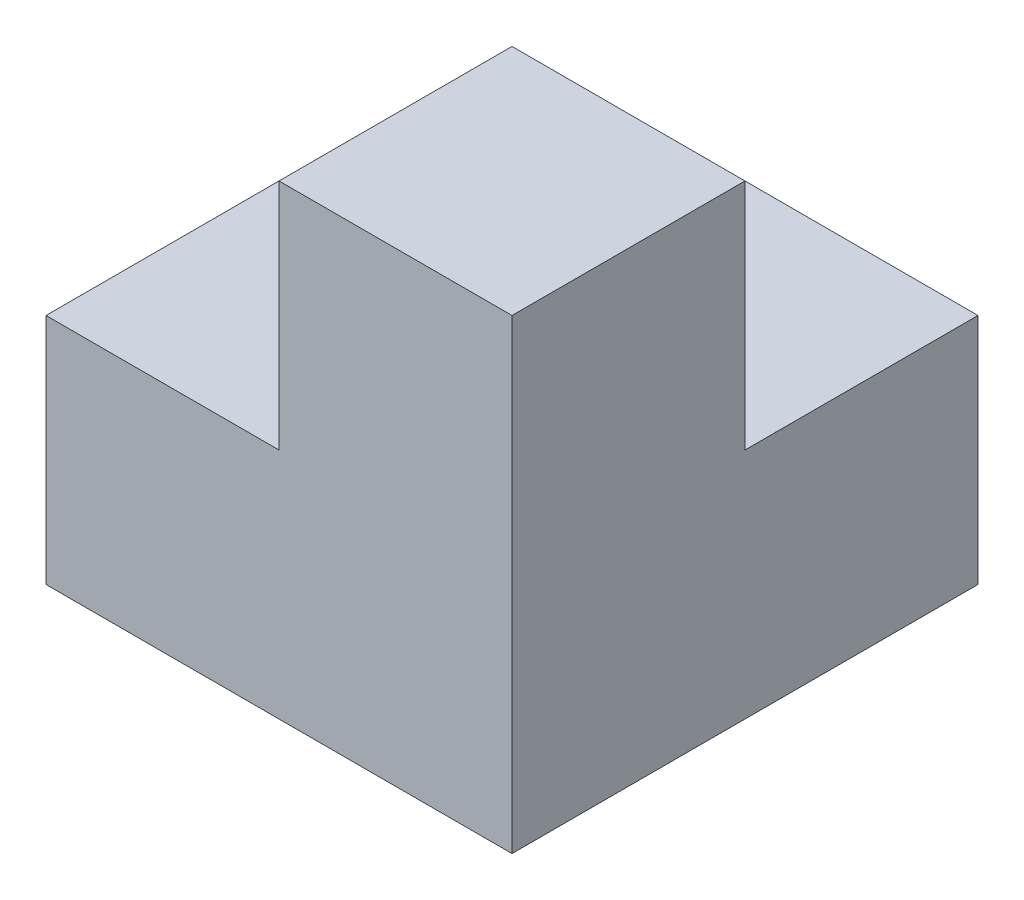
SolidWorks part; units mm, degrees
ref_plane "Front" through (0, 0, 0) normal (0, 0, 1) x (1, 0, 0)
ref_plane "Top" through (0, 0, 0) normal (0, 1, 0) x (1, 0, 0)
ref_plane "Right" through (0, 0, 0) normal (1, 0, 0) x (0, 0, -1)
sketch "Sketch1" plane through (0, 0, 0) normal (0, 1, 0) x (1, 0, 0)
  line L1 (0, 0) -> (4, 0)
  line L2 (0, 0) -> (0, 4)
  line L3 (0, 4) -> (4, 4)
  line L4 (4, 0) -> (4, 4)
  dimension "D1" = 4
  dimension "D2" = 4
extrude "Boss-Extrude1" add sketch "Sketch1" along normal blind 4
sketch "Sketch2" plane through (0, 4, 0) normal (0, 1, 0) x (1, 0, 0)
  line L5 (2, 2) -> (4, 2)
  line L6 (2, 2) -> (2, 0)
  line L7 (2, 0) -> (4, 0)
  line L8 (4, 2) -> (4, 0)
  line L10 (0, 0) -> (4, 0) construction
  point P4 (4, 0)
  point P5 (0, 0)
  point P6 (2, 0)
  line M1 (0, 4) -> (0, 0)
  line M2 (0, 0) -> (4, 0)
  line M3 (4, 0) -> (4, 4)
  line M4 (4, 4) -> (0, 4)
extrude "Cut-Extrude1" cut sketch "Sketch2" against normal blind 2 contours L8 L7 M4 M1 M2 M3
